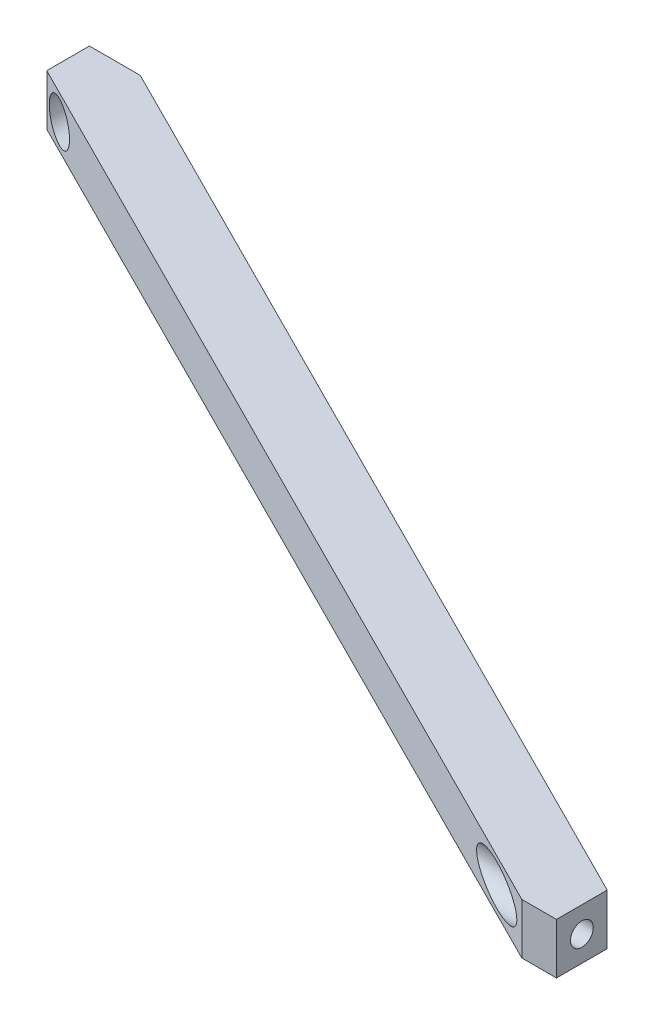
SolidWorks part; units mm, degrees
material "3.1325 (EN-AW 2017A)"
ref_plane "Face" through (0, 0, 0) normal (0, 0, 1) x (1, 0, 0)
ref_plane "Dessus" through (0, 0, 0) normal (0, 1, 0) x (1, 0, 0)
ref_plane "Droite" through (0, 0, 0) normal (1, 0, 0) x (0, 0, -1)
sketch "Esquisse1" plane through (0, 0, 0) normal (0, 1, 0) x (1, 0, 0)
  line L0 (-235, -22) -> (-235, -30.4039)
  line L3 (-46.825, -125) -> (-40, -125)
  line L7 (-40, -115) -> (-40, -125)
  line L8 (-235, -22) -> (-225, -22)
  line L9 (-225, -22) -> (-40, -115)
  line L10 (-235, -30.4039) -> (-46.825, -125)
  line L13 (-230.3897, -32.7215) -> (-45.3897, -125.7215) construction
  dimension "D8" = 12
extrude "Boss.-Extru.1" add sketch "Esquisse1" along normal blind 10
sketch "Esquisse4" plane through (0, 0, 22) normal (0, 0, -1) x (-1, 0, 0)
  line L0 (235, 10) -> (235, 0) construction
  line L1 (225, 10) -> (235, 10) construction
  circle A0 centre (230, 5) radius 2.1
  dimension "D1" = 5
  dimension "D2" = 5
extrude "Enlèv. mat.-Extru.1" cut sketch "Esquisse4" against normal through all
hole_wizard "Dégagement M41" positions "Esquisse6" profile "Esquisse5" hole size "M4" standard "ISO" end condition through all
sketch "Esquisse6" plane through (-40, 0, 0) normal (1, 0, 0) x (0, 0, -1)
  line L0 (-115, 10) -> (-115, 0) construction
  line L1 (-125, 10) -> (-115, 10) construction
  point P0 (-120, 5)
  dimension "D1" = 5
  dimension "D2" = 5
sketch "Esquisse5" plane through (-40, 5, 120) normal (0, 1, 0) x (0, 0, -1)
  line L0 (0, 0) -> (0, 195)
  line L1 (0, 195) -> (2.25, 195)
  line L2 (2.25, 195) -> (2.25, 0)
  line L5 (2.25, 0) -> (0, 0)
  line L11 (0, -6.35) -> (0, 107.95) construction
  dimension "Diamètre du perçage jusqu'au prochain" = 4.5
  dimension "Profondeur du perçage jusqu'au prochain" = 195
ref_plane "Plan1" through (0, 0, 28) normal (0, 0, -1) x (-1, 0, 0)
sketch "Esquisse7" plane through (0, 0, 28) normal (0, 0, -1) x (-1, 0, 0)
  circle A0 centre (230, 5) radius 4
extrude "Enlèv. mat.-Extru.2" cut sketch "Esquisse7" against normal blind 12
ref_plane "Plan2" through (-46, 0, 0) normal (1, 0, 0) x (0, 0, -1)
sketch "Esquisse8" plane through (-46, 0, 0) normal (1, 0, 0) x (0, 0, -1)
  circle A0 centre (-120, 5) radius 4
extrude "Enlèv. mat.-Extru.3" cut sketch "Esquisse8" against normal blind 28
